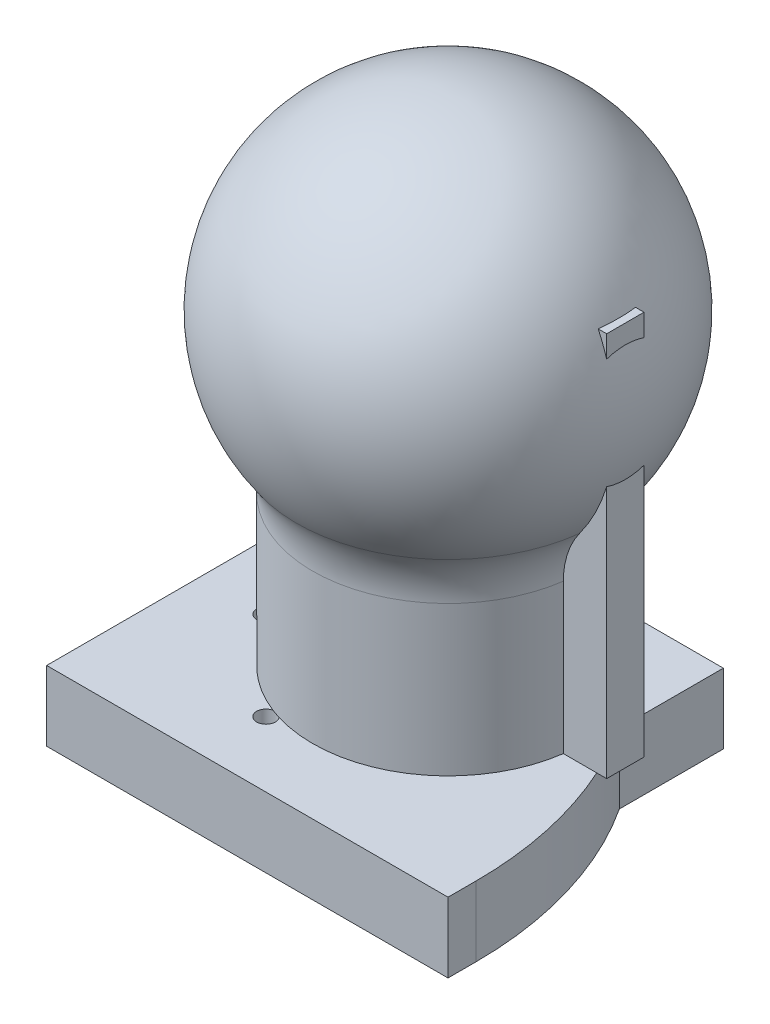
SolidWorks part; units mm, degrees
other "Markup1"
sketch "Sketch4" plane through (-40, 0, 40) normal (0, 0, 1) x (1, 0, 0)
ref_plane "Front Plane" through (0, 0, 0) normal (0, 0, 1) x (1, 0, 0)
ref_plane "Top Plane" through (0, 0, 0) normal (0, 1, 0) x (1, 0, 0)
ref_plane "Right Plane" through (0, 0, 0) normal (1, 0, 0) x (0, 0, -1)
sketch "Sketch1" plane through (0, 0, 0) normal (0, 1, 0) x (1, 0, 0)
  circle A0 centre (0, 0) radius 29
  dimension "D1" = 58
extrude "Boss-Extrude1" add sketch "Sketch1" along normal blind 32
sketch "Sketch2" plane through (0, 0, 0) normal (0, 0, 1) x (1, 0, 0)
  line L0 (0, 0) -> (0, 66) construction
  line L1 (-29, 32) -> (-29, 0) construction
  line L2 (29, 32) -> (-29, 32) construction
  line L3 (0, 66) -> (0, 106) construction
  line L4 (-29, 32) -> (0, 32)
  line L5 (0, 32) -> (0, 106)
  arc A0 (0, 106) -> (-32.4197, 42.5701) centre (0, 66) ccw
  arc A1 (-32.4197, 42.5701) -> (-29, 32) centre (-47.0455, 32) cw
  dimension "D1" = 80
  dimension "D2" = 34
revolve "Revolve1" add sketch "Sketch2" angle 360 about L5
sketch "Sketch3" plane through (0, 0, 0) normal (1, 0, 0) x (0, 0, -1)
  line L0 (0, 106) -> (0, 0) construction
  line L1 (-29, 0) -> (29, 0) construction
  line L2 (4, 0) -> (-4, 0)
  line L3 (4, 0) -> (4, 82.55)
  line L4 (4, 82.55) -> (-4, 82.55)
  line L5 (-4, 0) -> (-4, 82.55)
  arc A0 (32.4197, 42.5701) -> (-32.4197, 42.5701) centre (0, 66) ccw construction
  point P12 (0, 82.55)
  dimension "D1" = 82.55
  dimension "D2" = 8
extrude "Boss-Extrude2" add sketch "Sketch3" along normal blind 38
sketch "Sketch5" plane through (0, 0, 0) normal (1, 0, 0) x (0, 0, -1)
  line L0 (29, 0) -> (29, 32) construction
  line L1 (-29, 0) -> (29, 0)
  line L2 (-29, 0) -> (-29, -15)
  line L3 (-29, -15) -> (29, -15)
  line L4 (29, 0) -> (29, -15)
  dimension "D1" = 15
extrude "Boss-Extrude3" add sketch "Sketch5" along normal mid plane 60
sketch "Sketch6" plane through (0, -15, 0) normal (0, -1, 0) x (1, 0, 0)
  line L0 (0, 29) -> (0, -29) construction
  line L1 (-37, -43) -> (-43, -43)
  line L2 (43, 37) -> (43, 43)
  line L3 (43, 43) -> (-43, 43)
  line L4 (-43, -43) -> (-43, 43)
  line L5 (30, 29) -> (-30, 29) construction
  line L6 (30, -29) -> (-30, -29) construction
  arc A1 (-37, -43) -> (43, 37) centre (-37, 37) ccw
  point P4 (-43, 0)
  dimension "D2" = 80
  dimension "D1" = 86
extrude "Boss-Extrude4" add sketch "Sketch6" against normal up to surface (15 mm away) up to face at (-22.25, 0, 0)
sketch "Sketch7" plane through (0, 0, 0) normal (0, 1, 0) x (1, 0, 0)
  line L0 (-43, 43) -> (-43, -43) construction
  line L1 (-37, 43) -> (-43, 43) construction
  line L2 (-43, -43) -> (29, 29) construction
  line L3 (30, 29) -> (8.2106, 29) construction
  circle A0 centre (-29, -10) radius 2
  circle A1 centre (-10, -29) radius 2
  dimension "D2" = 4
  dimension "D1" = 14
  dimension "D3" = 53
  dimension "D4" = 45
extrude "Cut-Extrude2" cut sketch "Sketch7" against normal through all
